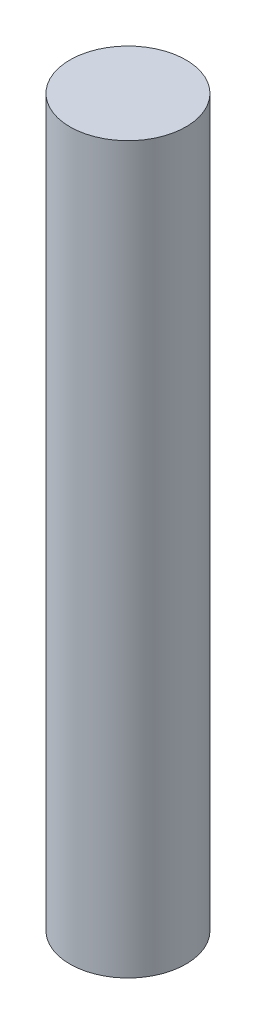
SolidWorks part; units mm, degrees
ref_plane "Front Plane" through (0, 0, 0) normal (0, 0, 1) x (1, 0, 0)
ref_plane "Top Plane" through (0, 0, 0) normal (0, 1, 0) x (1, 0, 0)
ref_plane "Right Plane" through (0, 0, 0) normal (1, 0, 0) x (0, 0, -1)
sketch "Sketch1" plane through (0, 0, 0) normal (0, 1, 0) x (1, 0, 0)
  circle A0 centre (0, 0) radius 4
  dimension "D1" = 8
extrude "Boss-Extrude1" add sketch "Sketch1" along normal blind 50
